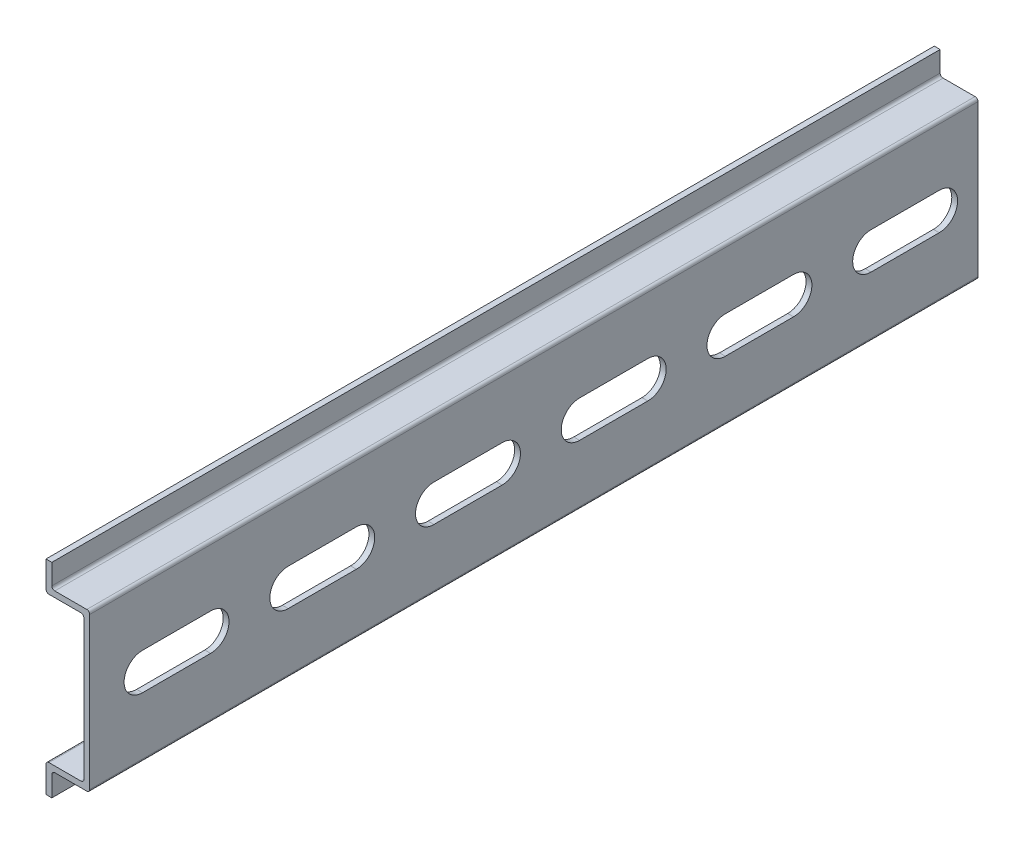
SolidWorks part; units mm, degrees
ref_plane "Front Plane" through (0, 0, 0) normal (0, 0, 1) x (1, 0, 0)
ref_plane "Top Plane" through (0, 0, 0) normal (0, 1, 0) x (1, 0, 0)
ref_plane "Right Plane" through (0, 0, 0) normal (1, 0, 0) x (0, 0, -1)
sketch "profile" plane through (0, 0, 0) normal (0, 0, 1) x (1, 0, 0)
  line L0 (0, -13.5) -> (0, 13.5) construction
  line L1 (0, 13.5) -> (-6.5, 13.5) construction
  line L2 (-6.5, 13.5) -> (-6.5, 17.5) construction
  line L3 (0, -13.5) -> (-6.5, -13.5) construction
  line L4 (-6.5, -13.5) -> (-6.5, -17.5) construction
  dimension "D1" = 27
  dimension "D2" = 35
  dimension "D3" = 6.5
sketch "Sketch3" plane through (0, 0, 0) normal (0, 0, 1) x (1, 0, 0)
  line L0 (-6.5, -13.5) -> (-6.5, -17.5) construction
  line L1 (0, -13.5) -> (-6.5, -13.5) construction
  line L2 (0, -13.5) -> (0, 13.5) construction
  line L3 (0, 13.5) -> (-6.5, 13.5) construction
  line L4 (-6.5, 13.5) -> (-6.5, 17.5) construction
  line L5 (-6.5, -13.5) -> (-6.5, -17.5)
  line L6 (0, -13.5) -> (-6.5, -13.5)
  line L7 (0, -13.5) -> (0, 13.5)
  line L8 (0, 13.5) -> (-6.5, 13.5)
  line L9 (-6.5, 13.5) -> (-6.5, 17.5)
extrude "Extrude-Thin1" add sketch "Sketch3" along normal blind 449.2625 thin
sketch "Sketch4" plane through (0, 0, 0) normal (1, 0, 0) x (0, 0, -1)
  line L0 (0, 0) -> (-62.1077, 0) construction
  line L1 (-6.65, 0) -> (-18.35, 0) construction
  line L2 (-6.65, -3.15) -> (-18.35, -3.15)
  line L3 (-6.65, 3.15) -> (-18.35, 3.15)
  arc A0 (-6.65, -3.15) -> (-6.65, 3.15) centre (-6.65, 0) ccw
  arc A1 (-18.35, 3.15) -> (-18.35, -3.15) centre (-18.35, 0) ccw
  point P5 (-12.5, 0)
  point P10 (-3.5, 0)
  point P11 (-21.5, 0)
  point P12 (-37.5, 0)
  dimension "D1" = 18
  dimension "D2" = 6.3
  dimension "D3" = 12.5
  dimension "D4" = 25
extrude "Cut-Extrude1" cut sketch "Sketch4" against normal through all both and the other way through all
pattern_linear "LPattern1" count 18 spacing 25 along (0, 0, 1) of "Cut-Extrude1"
fillet "Fillet1" radius 0.5 8 edges at (0, -13.5, 224.6312) (0, 13.5, 224.6312) (-6.5, 13.5, 224.6312) (-6.5, -13.5, 224.6312) (-1, 12.5, 224.6312) (-1, -12.5, 224.6312) (-7.5, -12.5, 224.6312) (-7.5, 12.5, 224.6312)
ref_plane "Contact Plane 1" through (-1, 0, 0) normal (-1, 0, 0) x (0, 0, 1)
sketch "Sketch5" plane through (0, 0, 449.2625) normal (0, 0, 1) x (1, 0, 0)
  line L1 (-16.1918, 21.4178) -> (7.3411, 21.4178)
  line L2 (-16.1918, 21.4178) -> (-16.1918, -23.0917)
  line L3 (-16.1918, -23.0917) -> (7.3411, -23.0917)
  line L4 (7.3411, 21.4178) -> (7.3411, -23.0917)
extrude "Cut-Extrude2" cut sketch "Sketch5" against normal blind 296.8625
equation "\"D3@LPattern1\"=\"D4@Sketch4\""
equation "\"D1@LPattern1\" = \"Length@Extrude-Thin1\" / \"D3@LPattern1\""
